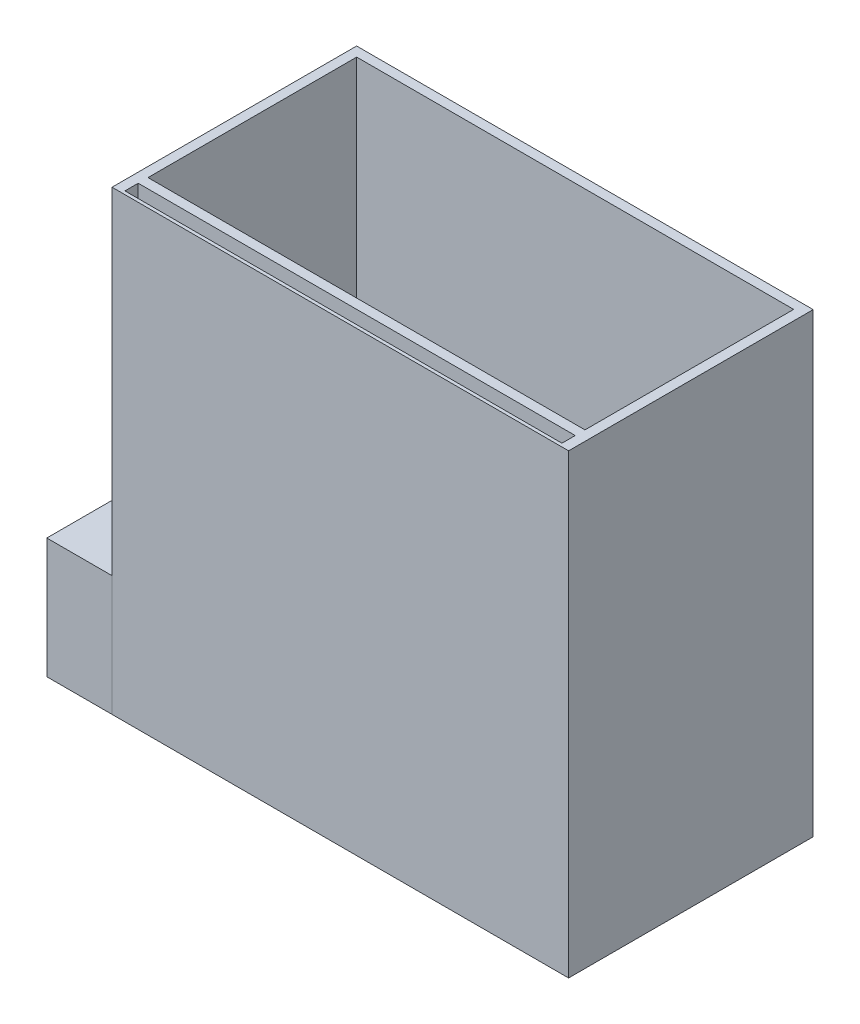
SolidWorks part; units mm, degrees
ref_plane "Front Plane" through (0, 0, 0) normal (0, 0, 1) x (1, 0, 0)
ref_plane "Top Plane" through (0, 0, 0) normal (0, 1, 0) x (1, 0, 0)
ref_plane "Right Plane" through (0, 0, 0) normal (1, 0, 0) x (0, 0, -1)
sketch "Sketch1" plane through (0, 0, 0) normal (0, 1, 0) x (1, 0, 0)
  line L1 (-116.8868, 58.0031) -> (23.1132, 58.0031)
  line L2 (-116.8868, 58.0031) -> (-116.8868, -11.9969)
  line L3 (-116.8868, -11.9969) -> (23.1132, -11.9969)
  line L4 (23.1132, 58.0031) -> (23.1132, -11.9969)
  line L5 (-116.8868, 58.0031) -> (23.1132, -11.9969) construction
  line L6 (-116.8868, -11.9969) -> (23.1132, 58.0031) construction
  point P0 (-46.8868, 23.0031)
  dimension "D1" = 70
  dimension "D2" = 140
extrude "Boss-Extrude1" add sketch "Sketch1" along normal blind 140 contours L4 L1 L2 L3
sketch "Sketch2" plane through (0, 140, 0) normal (0, 1, 0) x (1, 0, 0)
  line L1 (-113.9329, 55.0701) -> (20.0671, 55.0701)
  line L2 (-113.9329, 55.0701) -> (-113.9329, -8.9299)
  line L3 (-113.9329, -8.9299) -> (20.0671, -8.9299)
  line L4 (20.0671, 55.0701) -> (20.0671, -8.9299)
  dimension "D1" = 134
  dimension "D2" = 64
extrude "Cut-Extrude1" cut sketch "Sketch2" against normal blind 133
sketch "Sketch5" plane through (-116.8868, 0, 0) normal (-1, 0, 0) x (0, 0, 1)
  line L0 (-58.0031, 140) -> (-58.0031, 0) construction
  line L1 (-58.0031, 36.8465) -> (16.9971, 36.8465)
  line L2 (-58.0031, 36.8465) -> (-58.0031, 0)
  line L3 (-58.0031, 0) -> (16.9971, 0)
  line L4 (16.9971, 36.8465) -> (16.9971, 0)
extrude "Boss-Extrude3" add sketch "Sketch5" along normal blind 20
sketch "Sketch6" plane through (0, 0, -58.0031) normal (0, 0, -1) x (-1, 0, 0)
  line L0 (136.8868, 36.8465) -> (116.8868, 36.8465) construction
  line L1 (116.8868, 27.2465) -> (122.6368, 27.2465)
  line L2 (116.8868, 27.2465) -> (116.8868, 14.2465)
  line L3 (116.8868, 14.2465) -> (122.6368, 14.2465)
  line L4 (122.6368, 27.2465) -> (122.6368, 14.2465)
  line L5 (136.8868, 36.8465) -> (136.8868, 0) construction
  dimension "D1" = 13
  dimension "D2" = 5.75
  dimension "D3" = 9.6
  dimension "D4" = 14.25
extrude "Cut-Extrude2" cut sketch "Sketch6" against normal blind 3
sketch "Sketch9" plane through (0, 0, 11.9969) normal (0, 0, 1) x (1, 0, 0)
  line L0 (-133.8824, 36.8465) -> (-133.8824, 33.8465) construction
  line L1 (-136.8868, 36.8465) -> (-116.8868, 36.8465) construction
  line L2 (-136.8868, 33.8454) -> (-133.8868, 33.8454) construction
  line L3 (-136.8868, 0) -> (-136.8868, 36.8465) construction
  line L5 (-133.8824, 33.8465) -> (-116.8824, 33.8465)
  line L6 (-133.8824, 33.8465) -> (-133.8824, 2.9965)
  line L7 (-133.8824, 2.9965) -> (-116.8824, 2.9965)
  line L8 (-116.8824, 33.8465) -> (-116.8824, 2.9965)
  dimension "D1" = 3
  dimension "D2" = 3
  dimension "D3" = 17
  dimension "D4" = 30.85
extrude "Cut-Extrude3" cut sketch "Sketch9" against normal blind 67
sketch "Sketch11" plane through (0, 0, 11.9969) normal (0, 0, 1) x (1, 0, 0)
  line L0 (-46.8868, 140) -> (-46.8868, 0) construction
  line L1 (-116.8868, 140) -> (23.1132, 140)
  line L2 (-116.8868, 140) -> (-116.8868, 0)
  line L3 (-116.8868, 0) -> (23.1132, 0)
  line L4 (23.1132, 140) -> (23.1132, 0)
  line L5 (23.1132, 70) -> (-116.8868, 70) construction
extrude "Boss-Extrude5" add sketch "Sketch11" along normal blind 5
sketch "Sketch13" plane through (0, 0, 16.9969) normal (0, 0, 1) x (1, 0, 0)
sketch "Sketch15" plane through (0, 140, 0) normal (0, 1, 0) x (1, 0, 0)
  line L0 (-113.9329, -8.9299) -> (-113.9329, -11.9277) construction
  line L1 (-113.9329, -16.9969) -> (-113.9329, -16) construction
  line L2 (23.1132, -16.9969) -> (-116.8868, -16.9969) construction
  line L3 (20.0671, -8.9299) -> (20.0671, -11.9277) construction
  line L4 (-113.9329, -8.9299) -> (20.0671, -8.9299) construction
  line L5 (20.0671, -16.9969) -> (20.0671, -16) construction
  line L8 (20.0671, -11.9277) -> (-113.9329, -11.9277)
  line L9 (20.0671, -11.9277) -> (20.0671, -16)
  line L10 (20.0671, -16) -> (-113.9329, -16)
  line L11 (-113.9329, -11.9277) -> (-113.9329, -16)
extrude "Cut-Extrude4" cut sketch "Sketch15" against normal blind 137
